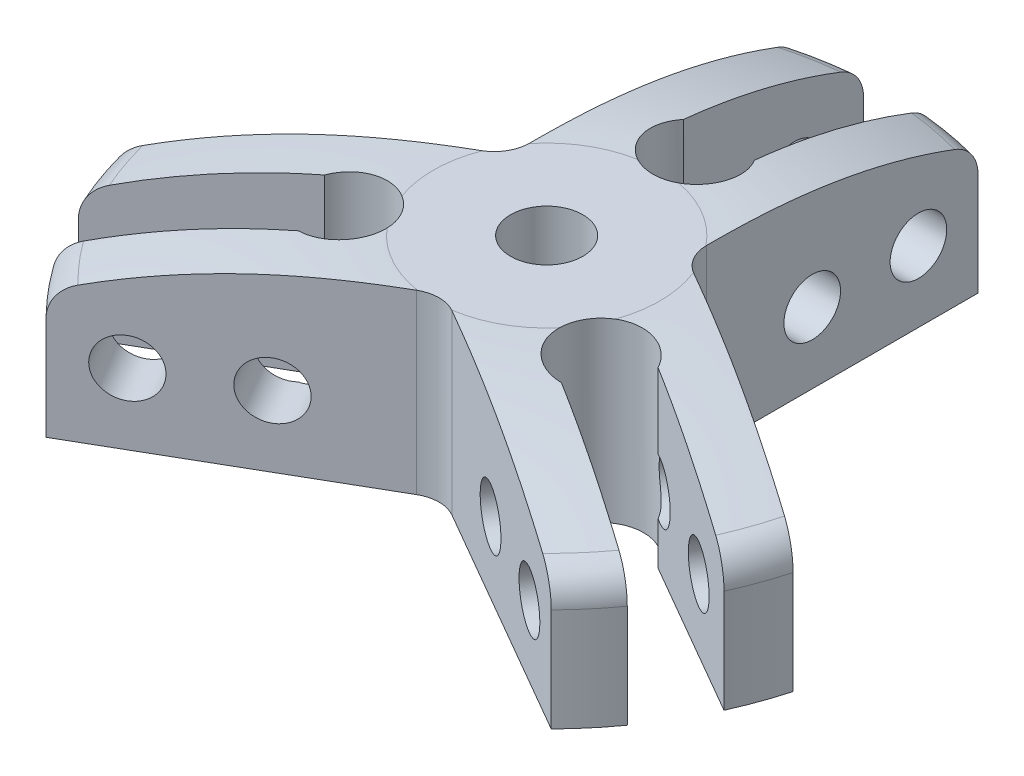
SolidWorks part; units mm, degrees
material "Acero aleado"
ref_plane "Alzado" through (0, 0, 0) normal (0, 0, 1) x (1, 0, 0)
ref_plane "Planta" through (0, 0, 0) normal (0, 1, 0) x (1, 0, 0)
ref_plane "Vista lateral" through (0, 0, 0) normal (1, 0, 0) x (0, 0, -1)
sketch "Croquis1" plane through (0, 0, 0) normal (0, 0, 1) x (1, 0, 0)
  line L0 (0, 0) -> (0, 25)
  line L1 (0, 25) -> (16, 25)
  line L2 (0, 0) -> (50, 0)
  line L3 (50, 0) -> (50, 14.5587)
  arc A0 (16, 25) -> (46.8125, 19.2186) centre (16, -60) cw
  arc A1 (50, 14.5587) -> (46.8125, 19.2186) centre (45, 14.5587) ccw
  dimension "D4" = 85
  dimension "D5" = 5
  dimension "D1" = 50
  dimension "D2" = 25
  dimension "D3" = 16
revolve "Revolución1" add sketch "Croquis1" angle 360 about L0
sketch "Croquis2" plane through (0, 0, 0) normal (0, 1, 0) x (1, 0, 0)
  line L0 (0, 0) -> (0, 72.5204) construction
  line L1 (0, 0) -> (75.3174, -43.4845) construction
  line L2 (15, 5.7735) -> (81.5674, -32.6592)
  line L3 (12.5, 10.1036) -> (12.5, 72.5204)
  line L4 (12.5, 7.2169) -> (81.5674, -32.6592) construction
  line L5 (12.5, 7.2169) -> (12.5, 72.5204) construction
  arc A0 (15, 5.7735) -> (12.5, 10.1036) centre (17.5, 10.1036) cw
  dimension "D3" = 5
  dimension "D1" = 120
  dimension "D2" = 12.5
extrude "Cortar-Extruir2" cut sketch "Croquis2" against normal through all and the other way through all flip side to cut
pattern_circular "MatrizC1" count 3 over 360 of "Cortar-Extruir2"
sketch "Croquis3" plane through (0, 0, 0) normal (0, -1, 0) x (1, 0, 0)
  line L0 (0, 0) -> (0, -56.6889) construction
  line L1 (-5, -24.3166) -> (-5, -58.4625)
  line L2 (5, -24.3166) -> (5, -58.4625)
  arc A0 (5, -24.3166) -> (-5, -24.3166) centre (0, -21) ccw
  dimension "D1" = 12
  dimension "D2" = 21
  dimension "D3" = 10
extrude "Cortar-Extruir4" cut sketch "Croquis3" against normal through all and the other way through all flip side to cut
sketch "Croquis4" plane through (12.5, 0, 0) normal (1, 0, 0) x (0, 0, -1)
  line L0 (10.1036, 0) -> (48.4123, 0) construction
  line L1 (0, 14.5587) -> (0, 0) construction
  circle A0 centre (25, 10) radius 4
  circle A1 centre (40, 10) radius 4
  dimension "D1" = 8
  dimension "D2" = 10
  dimension "D3" = 25
  dimension "D4" = 40
extrude "Cortar-Extruir5" cut sketch "Croquis4" against normal through all
pattern_circular "MatrizC2" count 3 over 360 of "Cortar-Extruir4", "Cortar-Extruir5"
hole_wizard "Taladro roscado M123" positions "Croquis12" profile "Croquis11" tap size "M12" standard "ISO" end condition through all
sketch "Croquis12" plane through (0, 25, 0) normal (0, 1, 0) x (1, 0, 0)
  point P0 (0, 0)
sketch "Croquis11" plane through (0, 25, 0) normal (1, 0, 0) x (0, 0, 1)
  line L0 (0, 0) -> (0, 25)
  line L1 (0, 25) -> (5.1, 25)
  line L2 (5.1, 25) -> (5.1, 0)
  line L5 (5.1, 0) -> (0, 0)
  line L11 (0, -6.35) -> (0, 107.95) construction
  dimension "Diámetro de perforador para roscar hasta el siguiente" = 10.2
  dimension "Profundidad de perforador para roscar hasta el siguiente" = 25
cosmetic thread "Rosca de taladro5" parameters "D2"=12
